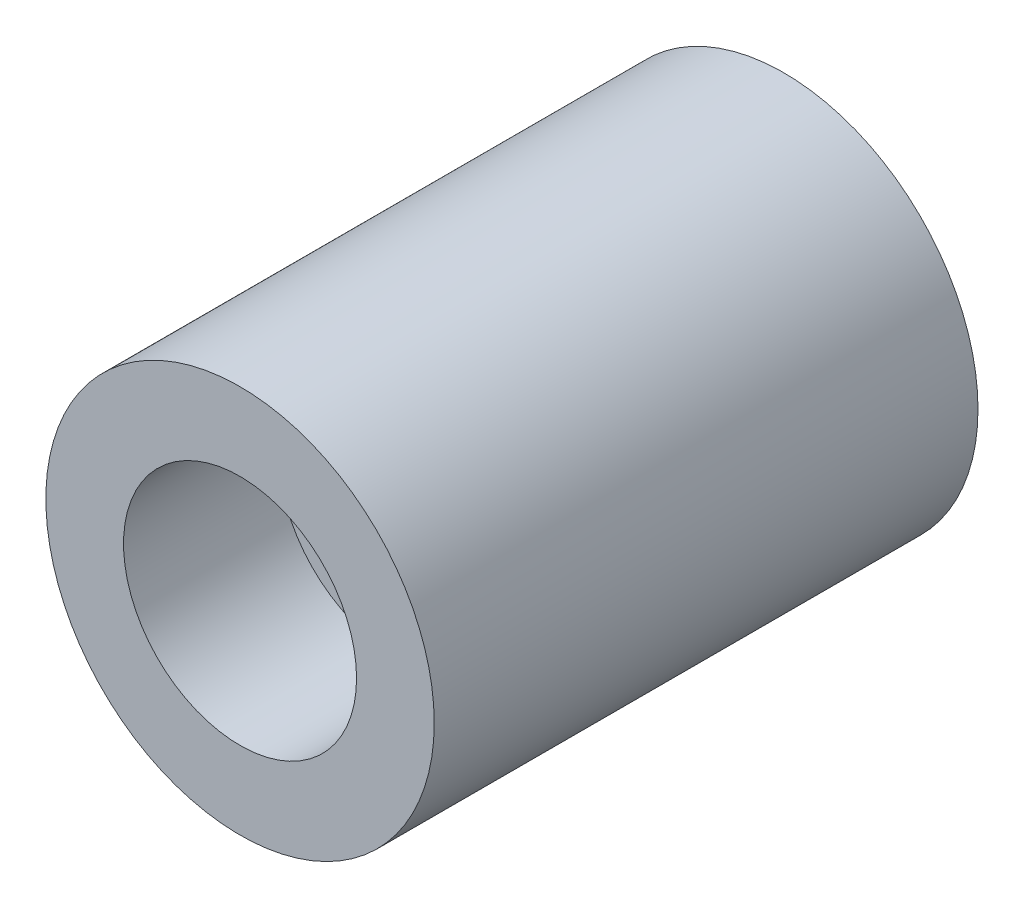
SolidWorks part; units mm, degrees
ref_plane "Front Plane" through (0, 0, 0) normal (0, 0, 1) x (1, 0, 0)
ref_plane "Top Plane" through (0, 0, 0) normal (0, 1, 0) x (1, 0, 0)
ref_plane "Right Plane" through (0, 0, 0) normal (1, 0, 0) x (0, 0, -1)
sketch "Sketch1" plane through (0, 0, 0) normal (0, 0, 1) x (1, 0, 0)
  circle A0 centre (0, 0) radius 1270
  dimension "D1" = 2540
extrude "Boss-Extrude1" add sketch "Sketch1" along normal blind 3556
sketch "Sketch2" plane through (0, 0, 3556) normal (0, 0, 1) x (1, 0, 0)
  circle A0 centre (0, 0) radius 762
  dimension "D1" = 1524
extrude "Cut-Extrude1" cut sketch "Sketch2" against normal blind 1016
sketch "Sketch3" plane through (0, 0, 3556) normal (0, 0, 1) x (1, 0, 0)
  circle A0 centre (0, 0) radius 254
  dimension "D1" = 508
extrude "Cut-Extrude2" cut sketch "Sketch3" against normal blind 3048
